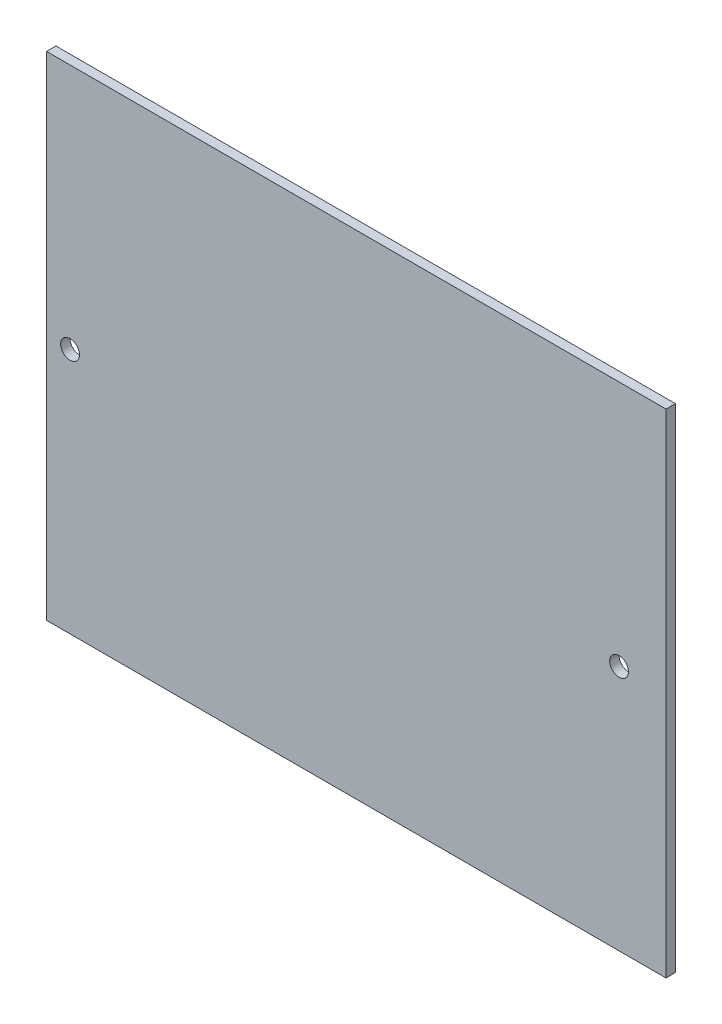
SolidWorks part; units mm, degrees
ref_plane "Front Plane" through (0, 0, 0) normal (0, 0, 1) x (1, 0, 0)
ref_plane "Top Plane" through (0, 0, 0) normal (0, 1, 0) x (1, 0, 0)
ref_plane "Right Plane" through (0, 0, 0) normal (1, 0, 0) x (0, 0, -1)
sketch "Sketch1" plane through (0, 0, 0) normal (0, 0, 1) x (1, 0, 0)
  line L0 (206.1201, 65.8579) -> (74.1201, 65.8579)
  line L1 (74.1201, 65.8579) -> (74.1201, -39.1421)
  line L2 (74.1201, -39.1421) -> (206.1201, -39.1421)
  line L3 (206.1201, -39.1421) -> (206.1201, 65.8579)
  dimension "D1" = 105
extrude "Boss-Extrude1" add sketch "Sketch1" along normal blind 2 contours L0 L1 L2 L3
sketch "Sketch2" plane through (0, 0, 0) normal (0, 0, -1) x (-1, 0, 0)
  line L0 (-206.1201, 13.3579) -> (-196.1201, 13.3579)
  line L1 (-206.1201, -39.1421) -> (-206.1201, 65.8579) construction
  circle A0 centre (-196.1201, 13.3579) radius 2
  dimension "D1" = 10
extrude "Cut-Extrude1" cut sketch "Sketch2" against normal blind 10 contours A0
sketch "Sketch3" plane through (0, 0, 0) normal (0, 0, -1) x (-1, 0, 0)
  line L0 (-74.1201, 13.3579) -> (-79.1201, 13.3579)
  line L1 (-74.1201, 65.8579) -> (-74.1201, -39.1421) construction
  circle A0 centre (-79.1201, 13.3579) radius 2
  dimension "D1" = 5
extrude "Cut-Extrude2" cut sketch "Sketch3" against normal blind 10 contours A0
